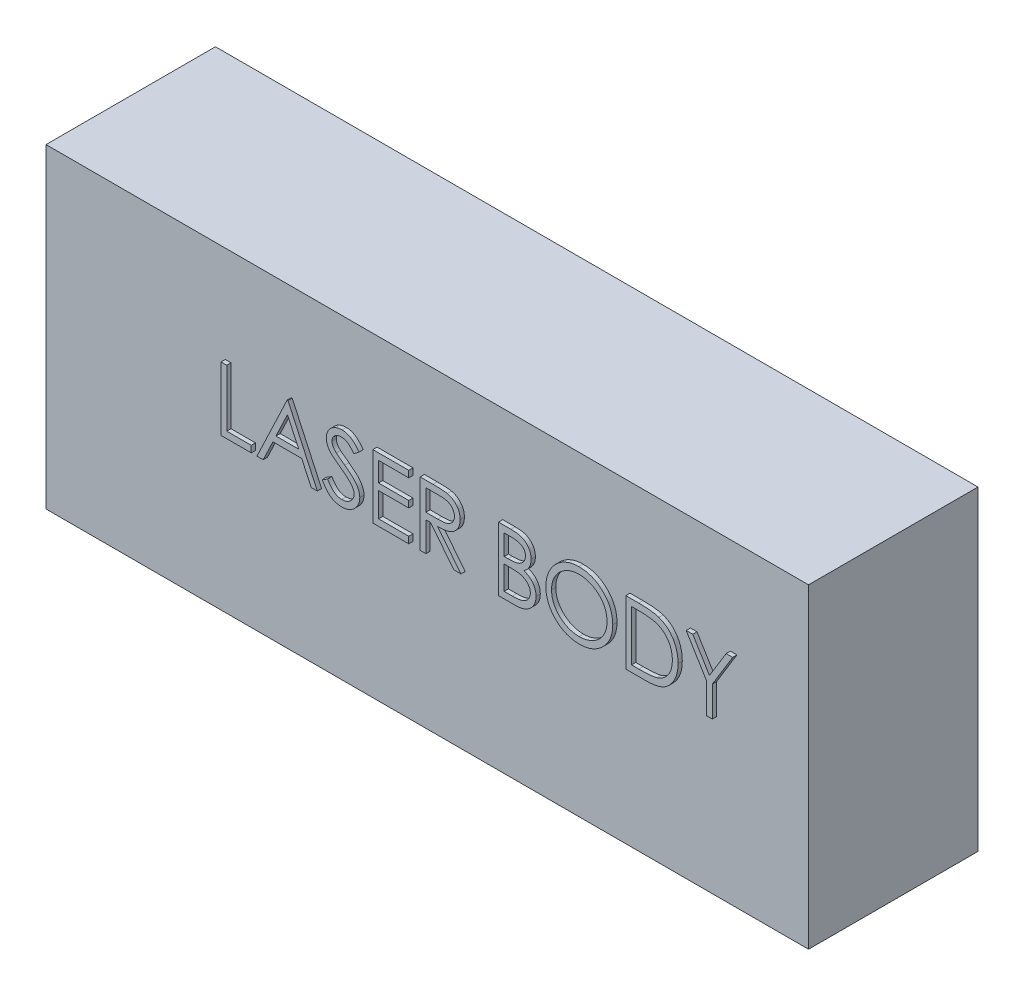
SolidWorks part; units mm, degrees
ref_plane "Front Plane" through (0, 0, 0) normal (0, 0, 1) x (1, 0, 0)
ref_plane "Top Plane" through (0, 0, 0) normal (0, 1, 0) x (1, 0, 0)
ref_plane "Right Plane" through (0, 0, 0) normal (1, 0, 0) x (0, 0, -1)
sketch "Sketch1" plane through (0, 0, 0) normal (0, 0, 1) x (1, 0, 0)
  line L1 (0, 0) -> (-3600, 0)
  line L2 (0, 0) -> (0, -1490)
  line L3 (0, -1490) -> (-3600, -1490)
  line L4 (-3600, 0) -> (-3600, -1490)
  text T0 "<b>MAIN LASER</b>" font "Century Gothic" height 319.05
  dimension "D1" = 3600
  dimension "D2" = 1490
extrude "Boss-Extrude1" add sketch "Sketch1" along normal blind 800 contours L1 L4 L3 L2
sketch "Sketch2" plane through (0, 0, 800) normal (0, 0, 1) x (1, 0, 0)
  text T0 "LASER BODY" font "Century Gothic" height 300.5
extrude "Boss-Extrude2" add sketch "Sketch2" against normal blind 1 and the other way blind 20
